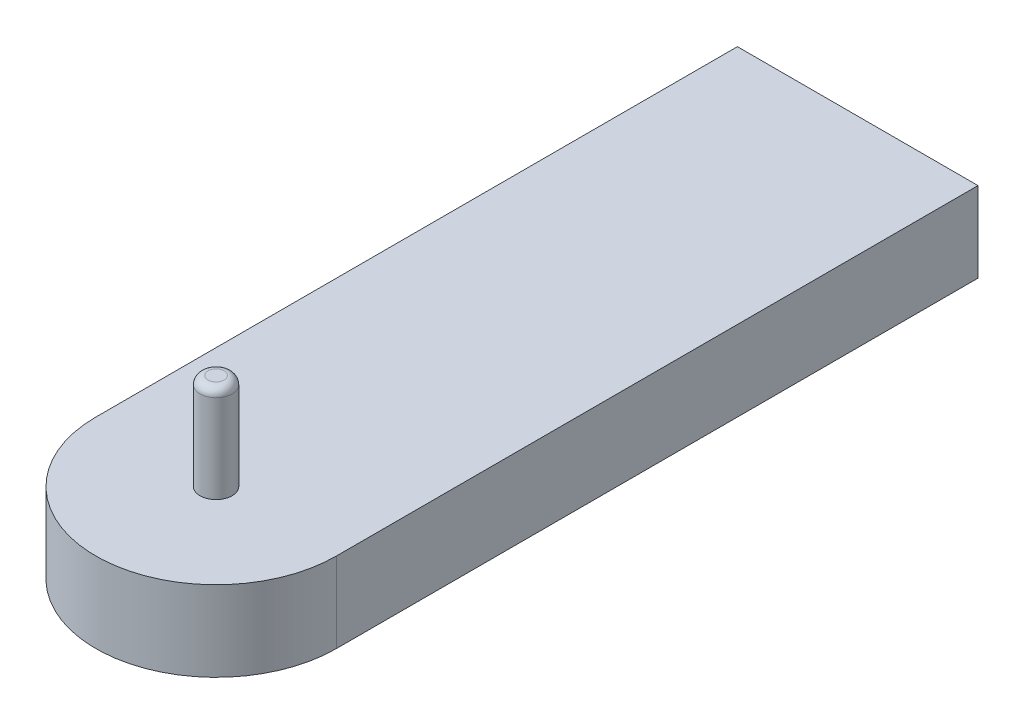
SolidWorks part; units mm, degrees
ref_plane "前视基准面" through (0, 0, 0) normal (0, 0, 1) x (1, 0, 0)
ref_plane "上视基准面" through (0, 0, 0) normal (0, 1, 0) x (1, 0, 0)
ref_plane "右视基准面" through (0, 0, 0) normal (1, 0, 0) x (0, 0, -1)
sketch "草图1" plane through (0, 0, 0) normal (0, 1, 0) x (1, 0, 0)
  line L1 (0, 0) -> (150, 0)
  line L2 (0, 0) -> (0, -400)
  line L3 (0, -400) -> (150, -400) construction
  line L4 (150, 0) -> (150, -400)
  arc A0 (0, -400) -> (150, -400) centre (75, -400) ccw
  dimension "D1" = 150
  dimension "D2" = 400
extrude "凸台-拉伸1" add sketch "草图1" along normal blind 50
sketch "草图2" plane through (0, 50, 0) normal (0, 1, 0) x (1, 0, 0)
  circle A0 centre (75, -400) radius 10
  dimension "D1" = 20
extrude "凸台-拉伸2" add sketch "草图2" along normal blind 60
fillet "圆角1" radius 5 1 edges at (75, 110, 410)
